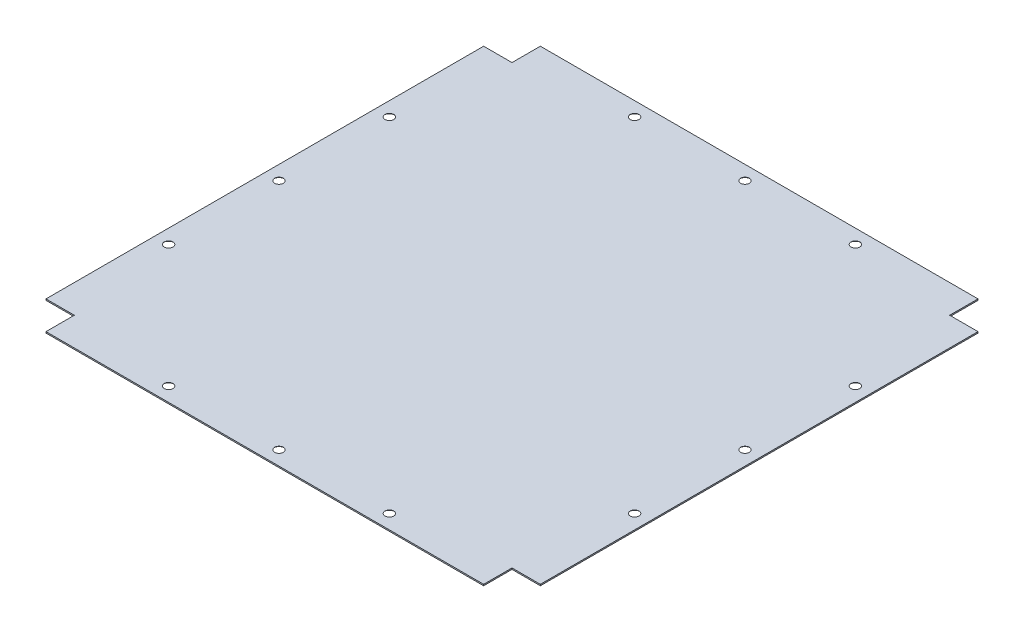
SolidWorks part; units mm, degrees
material "Acrylic (Medium-high impact)"
ref_plane "Front Plane" through (0, 0, 0) normal (0, 0, 1) x (1, 0, 0)
ref_plane "Top Plane" through (0, 0, 0) normal (0, 1, 0) x (1, 0, 0)
ref_plane "Right Plane" through (0, 0, 0) normal (1, 0, 0) x (0, 0, -1)
sketch "Sketch3" plane through (0, 0, 0) normal (0, 1, 0) x (1, 0, 0)
  line L0 (750, -43) -> (707, -43)
  line L1 (0, 0) -> (750, 0)
  line L2 (0, 0) -> (0, -750)
  line L3 (0, -750) -> (750, -750)
  line L4 (750, 0) -> (750, -750)
  line L5 (0, 0) -> (750, -750) construction
  line L6 (0, -750) -> (750, 0) construction
  line L7 (0, 0) -> (43, 0)
  line L8 (0, 0) -> (0, -43)
  line L9 (0, -43) -> (43, -43)
  line L10 (43, 0) -> (43, -43)
  line L11 (0, 0) -> (43, -43) construction
  line L12 (0, -43) -> (43, 0) construction
  line L13 (707, 0) -> (707, -43)
  line L14 (707, -750) -> (707, -707)
  line L15 (750, -707) -> (707, -707)
  line L16 (0, -707) -> (43, -707)
  line L17 (43, -750) -> (43, -707)
  point P4 (375, -375)
  point P9 (21.5, -21.5)
  point P10 (0, 0)
  point P22 (375, -375)
  dimension "D1" = 750
  dimension "D2" = 750
  dimension "D3" = 43
  dimension "D4" = 4
extrude "Boss-Extrude2" add sketch "Sketch3" along normal blind 2 contours L17 L3 L14 L15 L4 L0 L13 L1 L10 L9 L2 L16
sketch "Sketch4" plane through (0, 0, 0) normal (0, -1, 0) x (1, 0, 0)
  line L0 (0, 43) -> (43, 43) construction
  line L1 (43, 707) -> (0, 707)
  line L2 (43, 707) -> (43, 43) construction
  line L3 (43, 43) -> (0, 43)
  line L4 (0, 707) -> (0, 43) construction
  line L5 (43, 707) -> (0, 43) construction
  line L6 (43, 43) -> (0, 707) construction
  line L7 (0, 43) -> (0, 707) construction
  line L9 (43, 750) -> (707, 750) construction
  line L10 (43, 750) -> (43, 707) construction
  line L11 (43, 707) -> (707, 707) construction
  line L12 (707, 750) -> (707, 707) construction
  line L13 (43, 750) -> (707, 707) construction
  line L14 (43, 707) -> (707, 750) construction
  point P4 (21.5, 375)
  point P13 (375, 728.5)
hole_wizard "CSK for M8 Flat Head Machine Screw1" positions "Sketch8" profile "Sketch9" countersink size "M8" standard "ANSI Metric" end condition through all
sketch "Sketch8" plane through (0, 0, 0) normal (0, -1, 0) x (-1, 0, 0)
  point P0 (-21.5, -375)
sketch "Sketch9" plane through (21.5, 0, 375) normal (1, 0, 0) x (0, 0, -1)
  line L0 (0, 0) -> (0, 2)
  line L1 (0, 2) -> (4.5, 2)
  line L2 (4.5, 2) -> (4.5, 4.15)
  line L3 (4.5, 4.15) -> (8.65, 0)
  line L5 (8.65, 0) -> (0, 0)
  line L6 (-4.5, 4.15) -> (-8.65, 0) construction
  line L11 (0, -6.35) -> (0, 107.95) construction
  dimension "Thru Hole Dia." = 9
  dimension "Thru Hole Depth" = 2
  dimension "Near C'Sink Dia." = 17.3
  dimension "Near C'Sink Angle" = 90
hole_wizard "CSK for M8 Flat Head Machine Screw2" positions "Sketch11" profile "Sketch12" countersink size "M8" standard "ANSI Metric" end condition through all
sketch "Sketch11" plane through (0, 0, 0) normal (0, -1, 0) x (-1, 0, 0)
  point P0 (-375, -728.5)
  point P3 (-542.5, -728.5)
  point P5 (-207.5, -728.5)
  point P7 (-21.5, -542.5)
  point P9 (-21.5, -207.5)
  dimension "D1" = 167.5
  dimension "D2" = 167.5
  dimension "D3" = 167.5
  dimension "D4" = 167.5
sketch "Sketch12" plane through (375, 0, 728.5) normal (1, 0, 0) x (0, 0, -1)
  line L0 (0, 0) -> (0, 2)
  line L1 (0, 2) -> (4.5, 2)
  line L2 (4.5, 2) -> (4.5, 4.15)
  line L3 (4.5, 4.15) -> (8.65, 0)
  line L5 (8.65, 0) -> (0, 0)
  line L6 (-4.5, 4.15) -> (-8.65, 0) construction
  line L11 (0, -6.35) -> (0, 107.95) construction
  dimension "Thru Hole Dia." = 9
  dimension "Thru Hole Depth" = 2
  dimension "Near C'Sink Dia." = 17.3
  dimension "Near C'Sink Angle" = 90
ref_plane "Plane1" through (0, 0, 375) normal (0, 0, 1) x (1, 0, 0)
ref_plane "Plane2" through (375, 0, 0) normal (-1, 0, 0) x (0, 0, 1)
mirror "Mirror1" about plane through (375, 0, 0) normal (-1, 0, 0) of "CSK for M8 Flat Head Machine Screw1", "CSK for M8 Flat Head Machine Screw2"
mirror "Mirror2" about plane through (0, 0, 375) normal (0, 0, 1) of "CSK for M8 Flat Head Machine Screw2"
